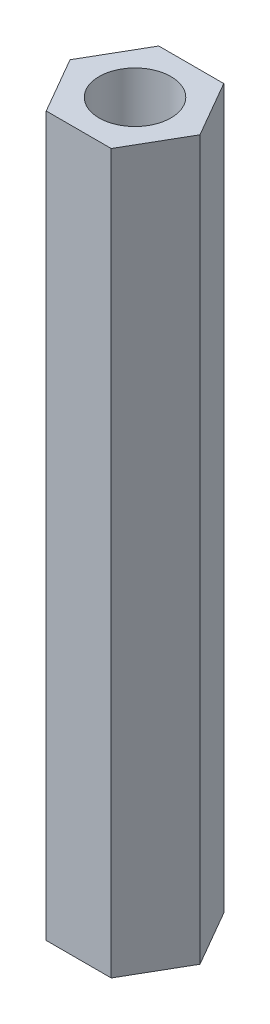
SolidWorks part; units mm, degrees
material "黄铜"
ref_plane "前视基准面" through (0, 0, 0) normal (0, 0, 1) x (1, 0, 0)
ref_plane "上视基准面" through (0, 0, 0) normal (0, 1, 0) x (1, 0, 0)
ref_plane "右视基准面" through (0, 0, 0) normal (1, 0, 0) x (0, 0, -1)
sketch "草图1" plane through (0, 0, 0) normal (0, 1, 0) x (1, 0, 0)
  line L1 (2.7135, 0) -> (1.3568, 2.35)
  line L2 (1.3568, 2.35) -> (-1.3568, 2.35)
  line L3 (-1.3568, 2.35) -> (-2.7135, 0)
  line L4 (-2.7135, 0) -> (-1.3568, -2.35)
  line L5 (-1.3568, -2.35) -> (1.3568, -2.35)
  line L6 (1.3568, -2.35) -> (2.7135, 0)
  circle A0 centre (0, 0) radius 2.35 construction
  circle A1 centre (0, 0) radius 1.5
  dimension "D2" = 3
  dimension "D1" = 4.7
extrude "凸台-拉伸1" add sketch "草图1" along normal blind 30
